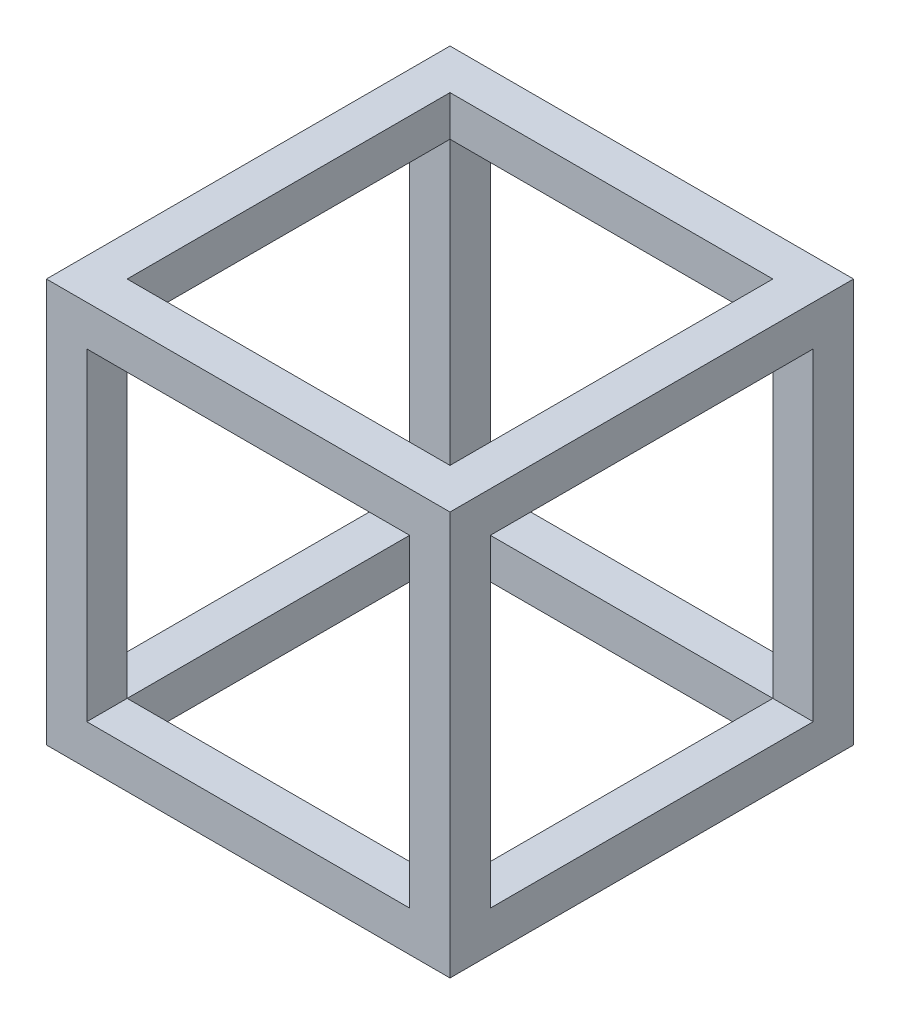
SolidWorks part; units mm, degrees
ref_plane "Front Plane" through (0, 0, 0) normal (0, 0, 1) x (1, 0, 0)
ref_plane "Top Plane" through (0, 0, 0) normal (0, 1, 0) x (1, 0, 0)
ref_plane "Right Plane" through (0, 0, 0) normal (1, 0, 0) x (0, 0, -1)
sketch "Szkic2" plane through (0, 0, 0) normal (0, 0, 1) x (1, 0, 0)
  line L1 (0, 0) -> (100, 0)
  line L2 (0, 0) -> (0, 100)
  line L3 (0, 100) -> (100, 100)
  line L4 (100, 0) -> (100, 100)
  dimension "D1" = 100
  dimension "D2" = 100
extrude "Dodanie-wyciągnięcie1" add sketch "Szkic2" along normal blind 100
sketch "Szkic3" plane through (0, 0, 100) normal (0, 0, 1) x (1, 0, 0)
  line L0 (0, 100) -> (0, 0) construction
  line L1 (10, 10) -> (90, 10)
  line L2 (10, 10) -> (10, 90)
  line L3 (10, 90) -> (90, 90)
  line L4 (90, 10) -> (90, 90)
  line L5 (100, 100) -> (0, 100) construction
  point P8 (10, 10.768)
  dimension "D1" = 10
  dimension "D2" = 10
  dimension "D3" = 80
  dimension "D4" = 80
extrude "Wytnij-wyciągnięcie1" cut sketch "Szkic3" against normal through all
sketch "Szkic4" plane through (100, 0, 0) normal (1, 0, 0) x (0, 0, -1)
  line L0 (-100, 100) -> (0, 100) construction
  line L1 (-90, 10) -> (-10, 10)
  line L2 (-90, 10) -> (-90, 90)
  line L3 (-90, 90) -> (-10, 90)
  line L4 (-10, 10) -> (-10, 90)
  line L5 (-90, 10) -> (-10, 90) construction
  line L6 (-90, 90) -> (-10, 10) construction
  line L7 (-100, 0) -> (-100, 100) construction
  point P0 (-50, 50)
  dimension "D1" = 80
  dimension "D2" = 80
  dimension "D3" = 10
  dimension "D4" = 10
extrude "Wytnij-wyciągnięcie2" cut sketch "Szkic4" against normal through all
sketch "Szkic6" plane through (0, 100, 0) normal (0, 1, 0) x (1, 0, 0)
  line L8 (10, -90) -> (90, -90)
  line L9 (90, -90) -> (90, -10)
  line L10 (90, -10) -> (10, -10)
  line L11 (10, -10) -> (10, -90)
  line L12 (10, -90) -> (90, -90)
  line L13 (90, -90) -> (90, -10)
  line L14 (90, -10) -> (10, -10)
  line L15 (10, -10) -> (10, -90)
  dimension "D1" = 10
extrude "Wytnij-wyciągnięcie3" cut sketch "Szkic6" against normal through all
sketch "Szkic7" plane through (0, 100, 0) normal (0, 1, 0) x (1, 0, 0)
  line L0 (10, -10) -> (90, -90) construction
  line L1 (90, -90) -> (43.812, -10) construction
  line L2 (90, -10) -> (10, -10) construction
  line L3 (90, -90) -> (90, -10) construction
  dimension "D1" = 30
ref_plane "Płaszczyzna 45*" through (0, 0, 0) normal (-0.7071, 0, 0.7071) x (0.7071, 0, 0.7071)
ref_plane "Płaszczyzna 30*" through (28.5289, 0, -16.4711) normal (-0.866, 0, 0.5) x (0.5, 0, 0.866)
